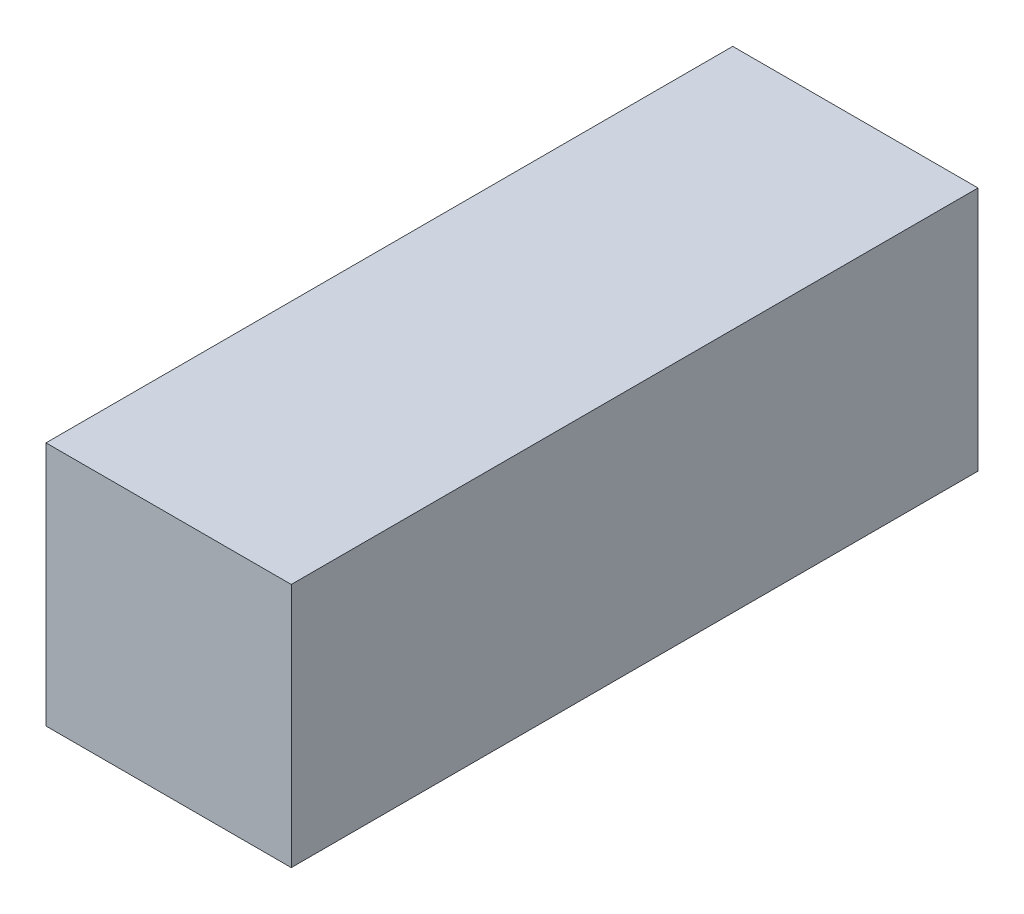
SolidWorks part; units mm, degrees
ref_plane "Front Plane" through (0, 0, 0) normal (0, 0, 1) x (1, 0, 0)
ref_plane "Top Plane" through (0, 0, 0) normal (0, 1, 0) x (1, 0, 0)
ref_plane "Right Plane" through (0, 0, 0) normal (1, 0, 0) x (0, 0, -1)
sketch "Sketch1" plane through (0, 0, 0) normal (0, 0, 1) x (1, 0, 0)
  line L1 (0, 0) -> (-50, 0)
  line L2 (0, 0) -> (0, 50)
  line L3 (0, 50) -> (-50, 50)
  line L4 (-50, 0) -> (-50, 50)
  dimension "D1" = 50
  dimension "D2" = 50
extrude "Boss-Extrude1" add sketch "Sketch1" along normal blind 140
